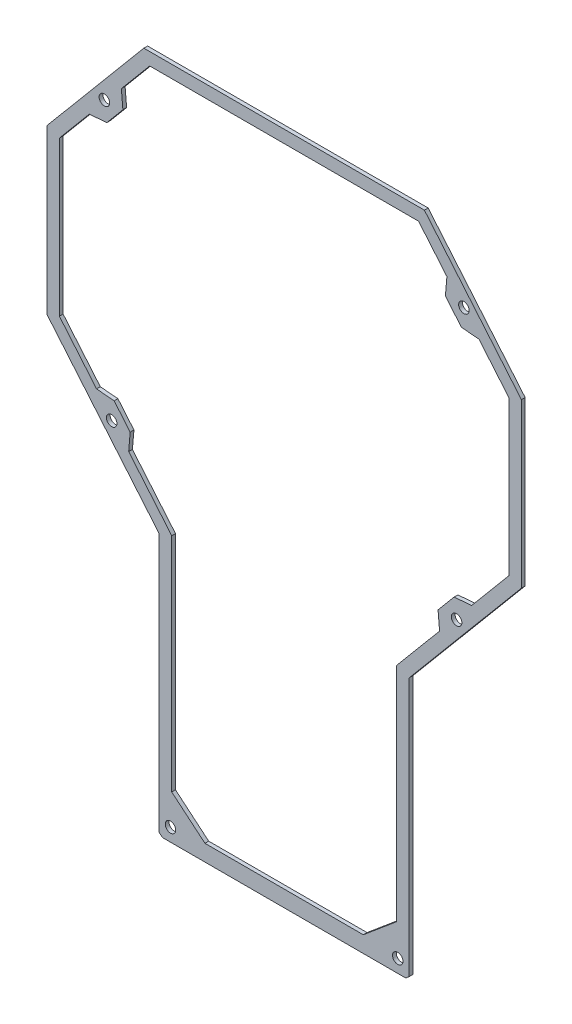
SolidWorks part; units mm, degrees
ref_plane "Plano frontal" through (0, 0, 0) normal (0, 0, 1) x (1, 0, 0)
ref_plane "Plano superior" through (0, 0, 0) normal (0, 1, 0) x (1, 0, 0)
ref_plane "Plano direito" through (0, 0, 0) normal (1, 0, 0) x (0, 0, -1)
sketch "Esboço1" plane through (0, 0, 0) normal (0, 0, 1) x (1, 0, 0)
  line L0 (56.4637, 135.1597) -> (-55.8644, 135.1597)
  line L1 (-55.8644, 135.1597) -> (-94.7003, 88.8768)
  line L2 (-94.7003, 88.8768) -> (-94.7003, 23.4903)
  line L3 (-94.7003, 23.4903) -> (-49.7003, -30.1386)
  line L4 (-49.7003, -30.1386) -> (-49.7003, -133.7325)
  line L5 (-49.7003, -133.7325) -> (-48.3802, -134.8403)
  line L6 (-48.3802, -134.8403) -> (48.9795, -134.8403)
  line L7 (50.2997, -133.7325) -> (48.9795, -134.8403)
  line L8 (50.2997, -30.1386) -> (50.2997, -133.7325)
  line L9 (95.2997, 23.4903) -> (50.2997, -30.1386)
  line L10 (95.2997, 88.8768) -> (95.2997, 23.4903)
  line L11 (56.4637, 135.1597) -> (95.2997, 88.8768)
  point P9 (0.2997, -134.8403)
  point P10 (0.2997, 135.1597)
extrude "Ressalto-extrusão1" add sketch "Esboço1" along normal blind 1.5
sketch "Esboço2" plane through (0, 0, 1.5) normal (0, 0, 1) x (1, 0, 0)
  line L0 (0.2997, -140.2297) -> (0.2997, 174.3695) construction
  line L1 (56.4637, 135.1597) -> (-55.8644, 135.1597) construction
  line L2 (-94.7003, 88.8768) -> (-94.7003, 23.4903) construction
  line L3 (-48.3802, -134.8403) -> (48.9795, -134.8403) construction
  line L5 (-94.7003, 23.4903) -> (-49.7003, -30.1386) construction
  line L8 (-49.7003, -30.1386) -> (-49.7003, -133.7325) construction
  line L9 (50.2997, -133.7325) -> (50.2997, -30.1386) construction
  circle A0 centre (-71.6727, 109.2987) radius 2.1
  circle A1 centre (-45.2003, -129.6103) radius 2.1
  circle A2 centre (45.7997, -129.6103) radius 2.1
  circle A3 centre (72.272, 109.2987) radius 2.1
  circle A4 centre (-68.7531, -0.4316) radius 2.1
  circle A5 centre (69.3525, -0.4316) radius 2.1
  dimension "D1" = 25.861
  dimension "D2" = 4.5
  dimension "D3" = 4.5
  dimension "D7" = 23.0276
  dimension "D8" = 5.23
  dimension "D4" = 4.5
extrude "Corte-extrusão1" cut sketch "Esboço2" against normal up to next
sketch "Esboço3" plane through (0, 0, 1.5) normal (0, 0, 1) x (1, 0, 0)
  line L0 (0.2997, -138.0724) -> (0.2997, 160.776) construction
  line L1 (-53.5328, 130.1597) -> (-64.8796, 116.6372)
  line L2 (-64.8796, 116.6372) -> (-64.2633, 109.5931)
  line L3 (-64.2633, 109.5931) -> (-70.6759, 101.9508)
  line L4 (-70.6759, 101.9508) -> (-77.7201, 101.3345)
  line L5 (-53.5328, 130.1597) -> (54.1321, 130.1597)
  line L6 (-89.7003, 87.057) -> (-89.7003, 25.3102)
  line L7 (-89.7003, 25.3102) -> (-74.79, 7.5407)
  line L8 (-77.7201, 101.3345) -> (-89.7003, 87.057)
  line L9 (-44.7003, -117.1732) -> (-31.4077, -128.3271)
  line L10 (-31.4077, -128.3271) -> (32.007, -128.3271)
  line L11 (-74.79, 7.5407) -> (-67.7458, 6.9244)
  line L12 (-67.7458, 6.9244) -> (-61.334, -0.7169)
  line L13 (-61.334, -0.7169) -> (-61.9503, -7.7611)
  line L14 (-61.9503, -7.7611) -> (-44.7003, -28.3187)
  line L15 (-94.7003, 23.4903) -> (-49.7003, -30.1386) construction
  line L17 (62.5496, -7.7611) -> (45.2997, -28.3187)
  line L18 (45.2997, -28.3187) -> (45.2997, -117.1732)
  line L19 (61.9333, -0.7169) -> (62.5496, -7.7611)
  line L20 (68.3451, 6.9244) -> (61.9333, -0.7169)
  line L21 (-49.7003, -133.7325) -> (-48.3802, -134.8403) construction
  line L22 (75.3893, 7.5407) -> (68.3451, 6.9244)
  line L23 (-94.7003, 88.8768) -> (-94.7003, 23.4903) construction
  line L24 (-55.8644, 135.1597) -> (-94.7003, 88.8768) construction
  line L25 (90.2997, 25.3102) -> (75.3893, 7.5407)
  line L28 (45.2997, -117.1732) -> (32.007, -128.3271)
  line L29 (78.3194, 101.3345) -> (90.2997, 87.057)
  line L31 (90.2997, 87.057) -> (90.2997, 25.3102)
  line L32 (71.2752, 101.9508) -> (78.3194, 101.3345)
  line L33 (64.8626, 109.5931) -> (71.2752, 101.9508)
  line L34 (65.4789, 116.6372) -> (64.8626, 109.5931)
  line L35 (54.1321, 130.1597) -> (65.4789, 116.6372)
  line L37 (-44.7003, -28.3187) -> (-44.7003, -117.1732)
  line L38 (-49.7003, -30.1386) -> (-49.7003, -133.7325) construction
  circle A1 centre (-71.6727, 109.2987) radius 2.1 construction
  circle A2 centre (-68.7531, -0.4316) radius 2.1 construction
  point P29 (0.2997, -128.3271)
  point P33 (0.2997, 130.1597)
  dimension "D6" = 10
  dimension "D12" = 10
  dimension "D13" = 10
  dimension "D4" = 45
  dimension "D9" = 10
  dimension "D14" = 10
  dimension "D2" = 5
  dimension "D3" = 5
  dimension "D5" = 5
  dimension "D7" = 10
  dimension "D8" = 5
  dimension "D10" = 45
  dimension "D11" = 45
  dimension "D15" = 45
  dimension "D18" = 5
extrude "Corte-extrusão2" cut sketch "Esboço3" against normal blind 10
